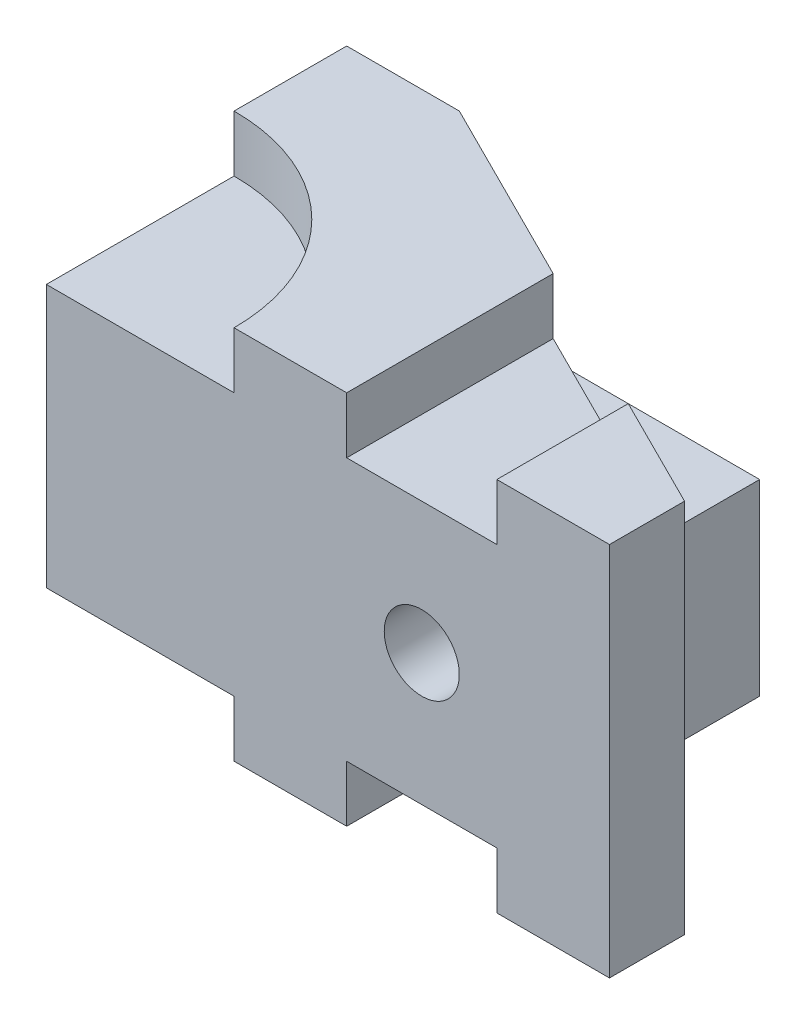
SolidWorks part; units mm, degrees
ref_plane "Front Plane" through (0, 0, 0) normal (0, 0, 1) x (1, 0, 0)
ref_plane "Top Plane" through (0, 0, 0) normal (0, 1, 0) x (1, 0, 0)
ref_plane "Right Plane" through (0, 0, 0) normal (1, 0, 0) x (0, 0, -1)
sketch "Sketch1" plane through (0, 0, 0) normal (0, 1, 0) x (1, 0, 0)
  line L0 (-45, 40) -> (-5, 20)
  line L1 (-75, -40) -> (75, -40)
  line L2 (-75, -40) -> (-75, 40)
  line L3 (-75, 40) -> (75, 40)
  line L4 (75, -40) -> (75, 40)
  line L5 (-75, -40) -> (75, 40) construction
  line L6 (-75, 40) -> (75, -40) construction
  line L7 (-5, 20) -> (55, 20)
  line L8 (55, 20) -> (55, -10)
  line L9 (55, -10) -> (75, -20)
  point P0 (0, 0)
  point P8 (20.575, 0)
  dimension "D1" = 80
  dimension "D2" = 150
  dimension "D3" = 20
  dimension "D4" = 30
  dimension "D5" = 20
  dimension "D6" = 30
extrude "Boss-Extrude1" add sketch "Sketch1" along normal blind 100 contours L9 L8 L7 L0 L3 L2 L1 L4
sketch "Sketch2" plane through (0, 100, 0) normal (0, 1, 0) x (1, 0, 0)
  line L0 (5, -40) -> (5, 15)
  line L1 (75, -40) -> (75, -20) construction
  line L2 (-75, -40) -> (75, -40) construction
  line L3 (5, 15) -> (45, -5)
  line L4 (45, -5) -> (45, -40)
  line L5 (-45, 40) -> (-5, 20) construction
  line L6 (45, -40) -> (5, -40)
  circle A0 centre (-75, -40) radius 50
  dimension "D1" = 100
  dimension "D2" = 40
  dimension "D3" = 30
extrude "Cut-Extrude1" cut sketch "Sketch2" against normal blind 15
sketch "Sketch3" plane through (0, 100, 0) normal (0, 1, 0) x (1, 0, 0)
  line L0 (-5, 20) -> (55, -10)
  line L1 (55, -10) -> (55, 20)
  line L2 (55, 20) -> (-5, 20)
extrude "Cut-Extrude2" cut sketch "Sketch3" against normal blind 25
ref_plane "Plane1" through (0, 50, 0) normal (0, 1, 0) x (1, 0, 0)
mirror "Mirror1" about plane through (0, 50, 0) normal (0, 1, 0) of "Cut-Extrude2", "Cut-Extrude1"
sketch "Sketch4" plane through (0, 0, -20) normal (0, 0, -1) x (-1, 0, 0)
  line L0 (5, 75) -> (5, 25) construction
  line L1 (5, 65) -> (75, 65)
  line L2 (5, 65) -> (5, 35)
  line L3 (5, 35) -> (75, 35)
  line L4 (75, 65) -> (75, 35)
  line L5 (75, 100) -> (75, 0) construction
  line L6 (75, 50) -> (34.9972, 50) construction
  line L7 (75, 50) -> (59.3043, 50) construction
  line L8 (44, 50) -> (-44, 50) construction
  line L9 (75, 100) -> (45, 100) construction
  dimension "D1" = 35
extrude "Cut-Extrude3" cut sketch "Sketch4" along normal through all
sketch "Sketch5" plane through (0, 0, -20) normal (0, 0, -1) x (-1, 0, 0)
  line L0 (44, 50) -> (-44, 50) construction
  line L1 (-55, 75) -> (-55, 25) construction
  circle A0 centre (-25, 50) radius 10
  dimension "D1" = 30
  dimension "D2" = 20
extrude "Cut-Extrude4" cut sketch "Sketch5" against normal through all
